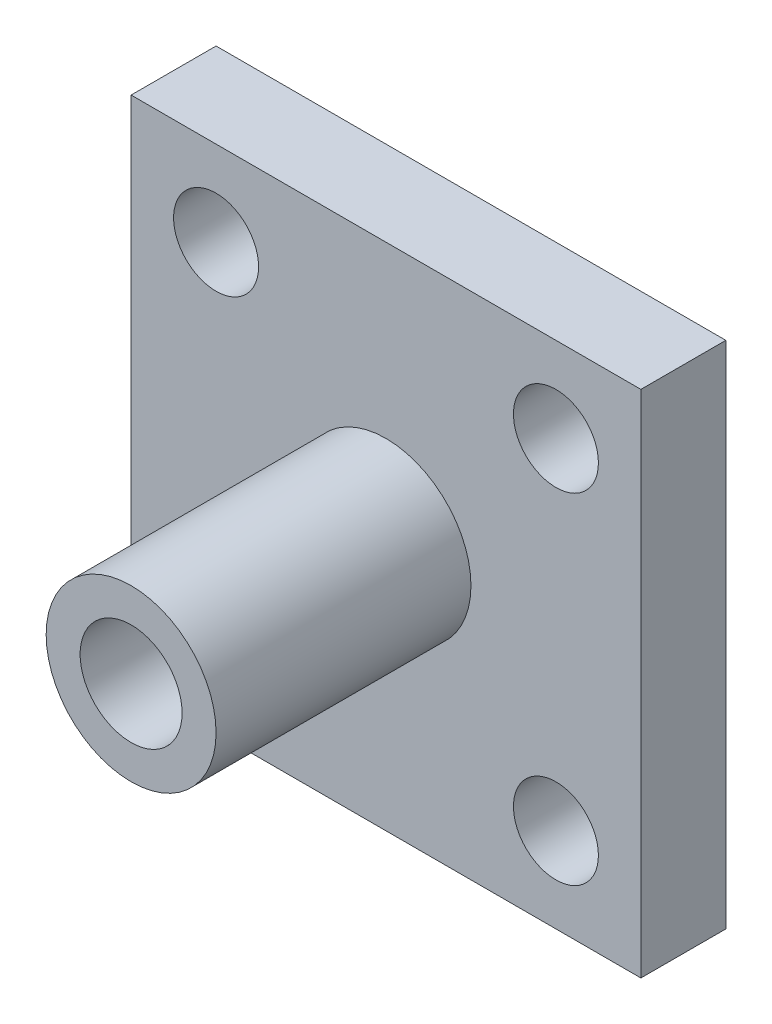
SolidWorks part; units mm, degrees
material "5052-O"
ref_plane "Plano frontal" through (0, 0, 0) normal (0, 0, 1) x (1, 0, 0)
ref_plane "Plano superior" through (0, 0, 0) normal (0, 1, 0) x (1, 0, 0)
ref_plane "Plano direito" through (0, 0, 0) normal (1, 0, 0) x (0, 0, -1)
sketch "Esboço1" plane through (0, 0, 0) normal (0, 0, 1) x (1, 0, 0)
  line L1 (-15, -15) -> (15, -15)
  line L2 (-15, -15) -> (-15, 15)
  line L3 (-15, 15) -> (15, 15)
  line L4 (15, -15) -> (15, 15)
  line L5 (-15, -15) -> (15, 15) construction
  line L6 (-15, 15) -> (15, -15) construction
  circle A0 centre (-10, 10) radius 2.5
  circle A1 centre (10, 10) radius 2.5
  circle A2 centre (10, -10) radius 2.5
  circle A3 centre (-10, -10) radius 2.5
  point P0 (0, 0)
  dimension "D3" = 5
  dimension "D4" = 5
  dimension "D5" = 5
  dimension "D6" = 5
  dimension "D1" = 30
  dimension "D2" = 30
  dimension "D7" = 5
  dimension "D8" = 5
  dimension "D9" = 5
  dimension "D10" = 5
extrude "Ressalto-extrusão1" add sketch "Esboço1" along normal blind 5
sketch "Esboço3" plane through (0, 0, 5) normal (0, 0, 1) x (1, 0, 0)
  circle A0 centre (0, 0) radius 5
  dimension "D1" = 10
extrude "Ressalto-extrusão2" add sketch "Esboço3" along normal blind 15
sketch "Esboço4" plane through (0, 0, 20) normal (0, 0, 1) x (1, 0, 0)
  circle A0 centre (0, 0) radius 3
  dimension "D1" = 6
extrude "Corte-extrusão1" cut sketch "Esboço4" against normal blind 15
sketch "Esboço5" plane through (0, 0, 0) normal (1, 0, 0) x (0, 0, -1)
  line L0 (-20, 5) -> (-20, -5) construction
  circle A0 centre (-8, 0) radius 2
  circle A1 centre (-14, 0) radius 2
  dimension "D1" = 4
  dimension "D2" = 12
  dimension "D4" = 4
  dimension "D3" = 6
extrude "Corte-extrusão2" cut sketch "Esboço5" against normal blind 15
